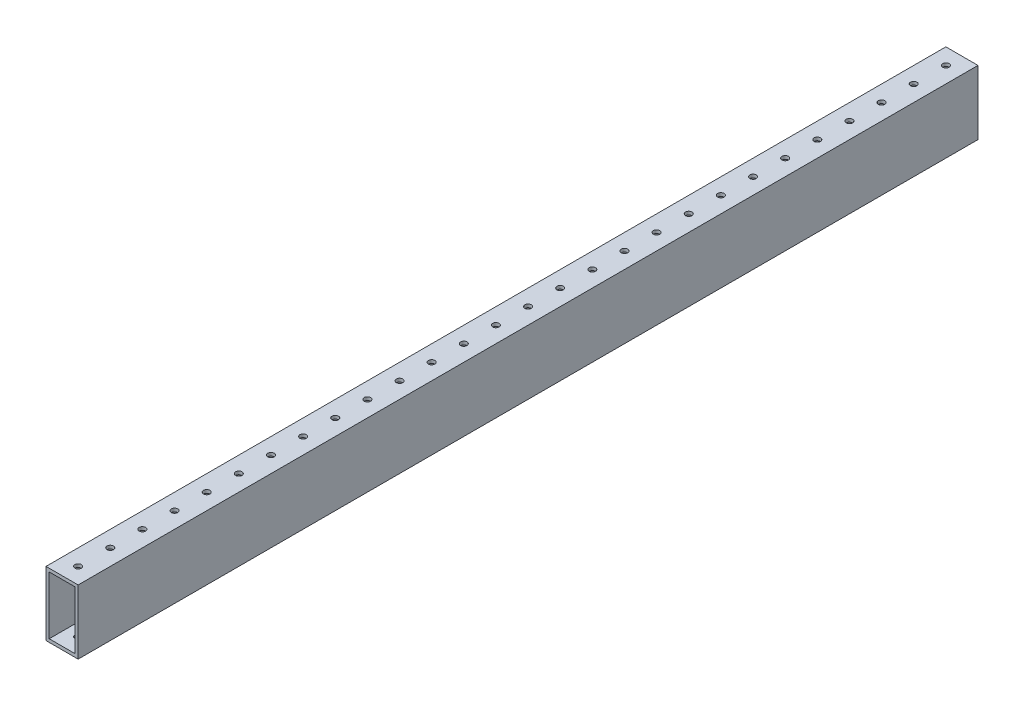
SolidWorks part; units mm, degrees
ref_plane "Front Plane" through (0, 0, 0) normal (0, 0, 1) x (1, 0, 0)
ref_plane "Top Plane" through (0, 0, 0) normal (0, 1, 0) x (1, 0, 0)
ref_plane "Right Plane" through (0, 0, 0) normal (1, 0, 0) x (0, 0, -1)
sketch "Sketch1" plane through (0, 0, 0) normal (0, 0, 1) x (1, 0, 0)
  line L0 (2.54, 48.26) -> (22.86, 48.26)
  line L1 (0, 0) -> (25.4, 0)
  line L2 (0, 0) -> (0, 50.8)
  line L3 (0, 50.8) -> (25.4, 50.8)
  line L4 (25.4, 0) -> (25.4, 50.8)
  line L5 (22.86, 2.54) -> (22.86, 48.26)
  line L6 (2.54, 2.54) -> (22.86, 2.54)
  line L7 (2.54, 2.54) -> (2.54, 48.26)
  dimension "D1" = 25.4
  dimension "D2" = 50.8
  dimension "D3" = 2.54
extrude "Boss-Extrude1" add sketch "Sketch1" along normal blind 711.2
sketch "Sketch2" plane through (0, 50.8, 0) normal (0, 1, 0) x (1, 0, 0)
  line L0 (25.4, -711.2) -> (0, -711.2) construction
  line L1 (25.4, -711.2) -> (25.4, 0) construction
  circle A0 centre (12.7, -698.5) radius 2.54
  dimension "D1" = 5.08
  dimension "D2" = 12.7
  dimension "D3" = 12.7
extrude "Cut-Extrude1" cut sketch "Sketch2" against normal through all
pattern_linear "LPattern1" count 28 spacing 25.4 along (0, 0, -1) of "Cut-Extrude1"
